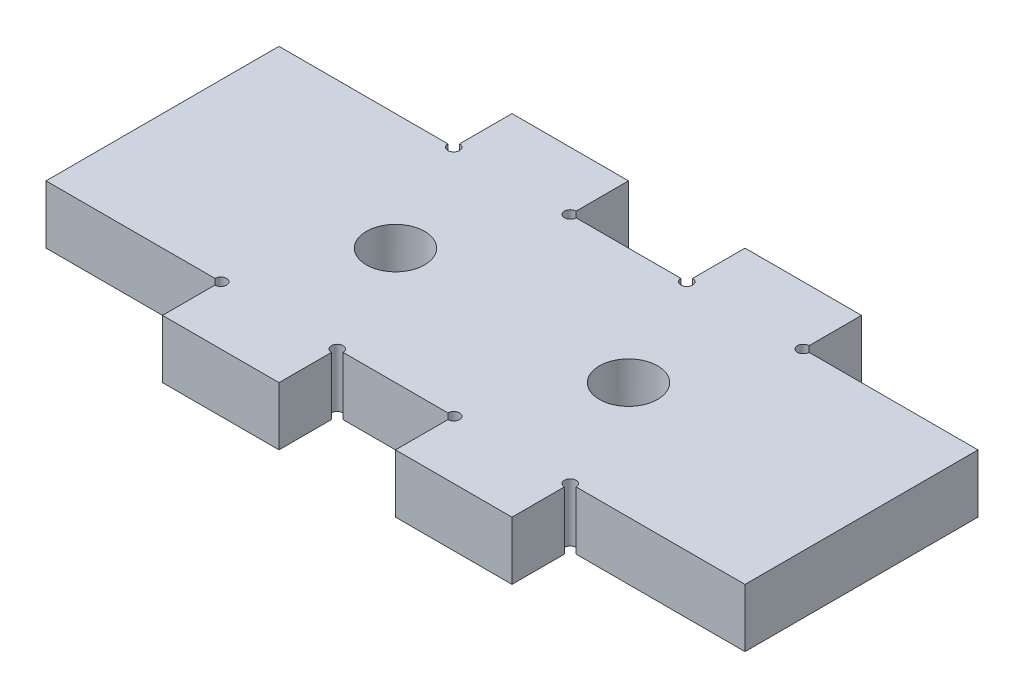
SolidWorks part; units mm, degrees
material "Acrylic (Medium-high impact)"
ref_plane "Front Plane" through (0, 0, 0) normal (0, 0, 1) x (1, 0, 0)
ref_plane "Top Plane" through (0, 0, 0) normal (0, 1, 0) x (1, 0, 0)
ref_plane "Right Plane" through (0, 0, 0) normal (1, 0, 0) x (0, 0, -1)
sketch "Sketch1" plane through (0, 0, 0) normal (0, 1, 0) x (1, 0, 0)
  line L0 (-19.05, 12.7) -> (-19.05, 19.05)
  line L1 (-38.1, 12.7) -> (-19.05, 12.7)
  line L2 (-38.1, 12.7) -> (-38.1, -12.7)
  line L3 (-38.1, -12.7) -> (-19.05, -12.7)
  line L4 (38.1, 12.7) -> (38.1, -12.7)
  line L5 (-38.1, 12.7) -> (38.1, -12.7) construction
  line L6 (-38.1, -12.7) -> (38.1, 12.7) construction
  line L7 (-19.05, 19.05) -> (-6.35, 19.05)
  line L8 (-6.35, 19.05) -> (-6.35, 12.7)
  line L9 (-6.35, 12.7) -> (6.35, 12.7)
  line L10 (0, -4.7893) -> (0, 19.05) construction
  line L11 (6.35, 19.05) -> (6.35, 12.7)
  line L12 (19.05, 19.05) -> (6.35, 19.05)
  line L13 (19.05, 12.7) -> (19.05, 19.05)
  line L14 (-8.6907, 0) -> (8.2657, 0) construction
  line L15 (-6.35, -19.05) -> (-6.35, -12.7)
  line L16 (-19.05, -19.05) -> (-6.35, -19.05)
  line L17 (-19.05, -12.7) -> (-19.05, -19.05)
  line L18 (19.05, -12.7) -> (19.05, -19.05)
  line L19 (19.05, -19.05) -> (6.35, -19.05)
  line L20 (6.35, -19.05) -> (6.35, -12.7)
  line L21 (19.05, 12.7) -> (38.1, 12.7)
  line L22 (19.05, -12.7) -> (38.1, -12.7)
  line L23 (-6.35, -12.7) -> (6.35, -12.7)
  point P0 (0, 0)
  dimension "D1" = 25.4
  dimension "D2" = 6.35
  dimension "D3" = 12.7
  dimension "D4" = 12.7
  dimension "D5" = 19.05
extrude "Boss-Extrude1" add sketch "Sketch1" along normal blind 6.35
sketch "Sketch2" plane through (0, 6.35, 0) normal (0, 1, 0) x (1, 0, 0)
  line L0 (-6.35, 19.05) -> (-19.05, 19.05) construction
  line L1 (19.05, 19.05) -> (6.35, 19.05) construction
  circle A0 centre (-12.7, 0) radius 3.175
  circle A1 centre (12.7, 0) radius 3.175
  point P7 (-12.7, 19.05)
  point P10 (12.7, 19.05)
  dimension "D1" = 6.35
  dimension "D2" = 6.35
extrude "Cut-Extrude1" cut sketch "Sketch2" against normal up to next
sketch "Sketch3" plane through (0, 6.35, 0) normal (0, 1, 0) x (1, 0, 0)
  point P0 (-19.05, 12.7)
  point P1 (-6.35, 12.7)
  point P3 (6.35, 12.7)
  point P5 (19.05, 12.7)
  point P7 (19.05, -12.7)
  point P9 (6.35, -12.7)
  point P11 (-6.35, -12.7)
  point P13 (-19.05, -12.7)
sketch "Sketch4" plane through (0, 6.35, 0) normal (0, 1, 0) x (1, 0, 0)
  circle A0 centre (-19.05, 12.7) radius 0.635
  dimension "D1" = 1.27
extrude "Cut-Extrude2" cut sketch "Sketch4" against normal up to next
pattern_sketch "Sketch-Pattern1" of "Cut-Extrude2" driven by "Sketch3"
